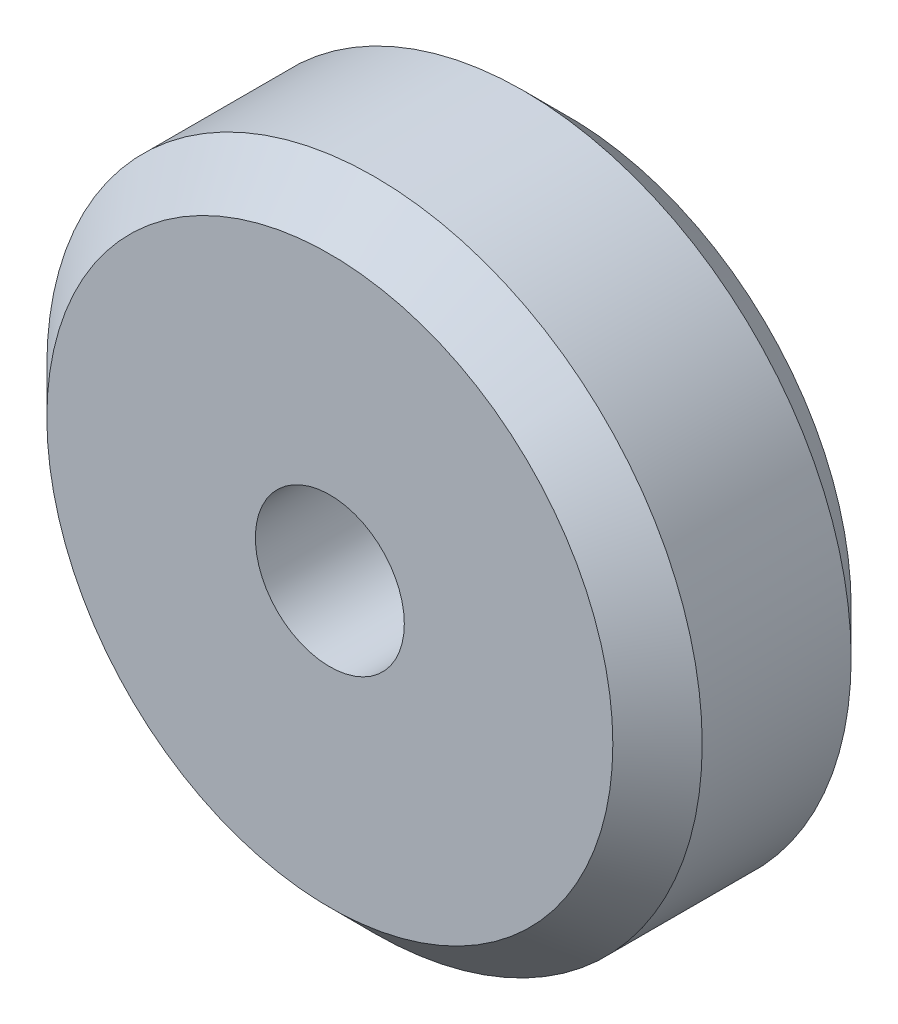
SolidWorks part; units mm, degrees
ref_plane "Front Plane" through (0, 0, 0) normal (0, 0, 1) x (1, 0, 0)
ref_plane "Top Plane" through (0, 0, 0) normal (0, 1, 0) x (1, 0, 0)
ref_plane "Right Plane" through (0, 0, 0) normal (1, 0, 0) x (0, 0, -1)
sketch "Sketch1" plane through (0, 0, 0) normal (0, 0, 1) x (1, 0, 0)
  circle A0 centre (0, 0) radius 2.5
  circle A1 centre (0, 0) radius 11
  dimension "7" = 5
  dimension "D2" = 22
extrude "Boss-Extrude1" add sketch "Sketch1" along normal mid plane 8
chamfer "Chamfer3" distance 1.5 angle 45 2 edges at (11, 0, -4) (11, 0, 4)
